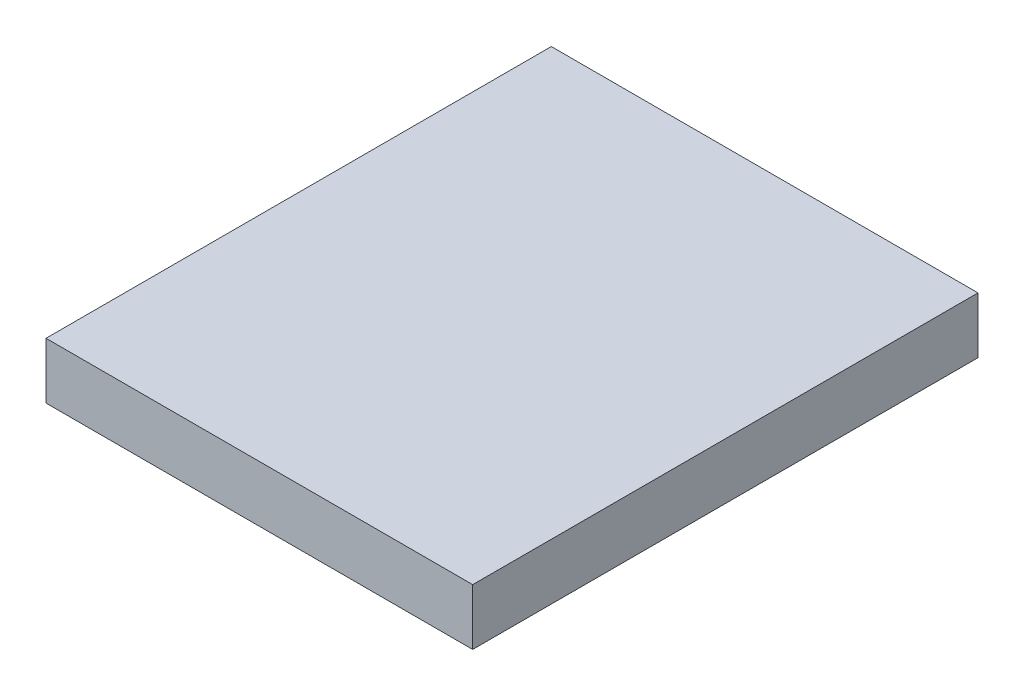
SolidWorks part; units mm, degrees
ref_plane "Frontal" through (0, 0, 0) normal (0, 0, 1) x (1, 0, 0)
ref_plane "Superior" through (0, 0, 0) normal (0, 1, 0) x (1, 0, 0)
ref_plane "Direito" through (0, 0, 0) normal (1, 0, 0) x (0, 0, -1)
sketch "Esboço1" plane through (0, 0, 0) normal (0, 1, 0) x (1, 0, 0)
  line L1 (-44.4009, 60.2217) -> (31.5991, 60.2217)
  line L2 (-44.4009, 60.2217) -> (-44.4009, -29.7783)
  line L3 (-44.4009, -29.7783) -> (31.5991, -29.7783)
  line L4 (31.5991, 60.2217) -> (31.5991, -29.7783)
  dimension "D1" = 90
  dimension "D2" = 76
extrude "Ressalto-extrusão1" add sketch "Esboço1" along normal blind 10
